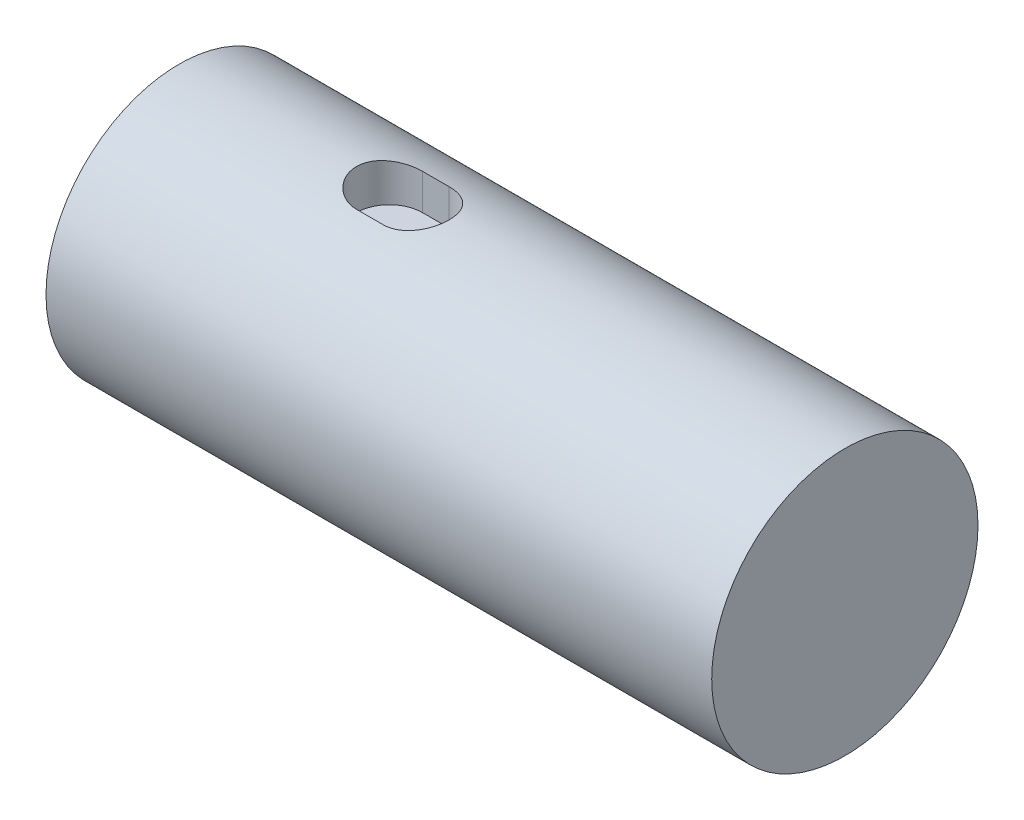
SolidWorks part; units mm, degrees
material "EN AW-AlMg4,5Mn0,7"
ref_plane "Přední rovina - XY" through (0, 0, 0) normal (0, 0, 1) x (1, 0, 0)
ref_plane "Horní rovina - XZ" through (0, 0, 0) normal (0, 1, 0) x (1, 0, 0)
ref_plane "Pravá rovina YZ" through (0, 0, 0) normal (1, 0, 0) x (0, 0, -1)
sketch "Skica1" plane through (0, 0, 0) normal (1, 0, 0) x (0, 0, -1)
  circle A0 centre (0, 0) radius 20
  point P3 (0, 20)
  dimension "D1" = 40
extrude "Vysunout1" add sketch "Skica1" along normal blind 100
ref_plane "Rovina1" through (0, 20, 0) normal (0, 1, 0) x (-1, 0, 0)
sketch "Skica2" plane through (0, 0, 0) normal (0, 1, 0) x (1, 0, 0)
  line L0 (31.5938, 0) -> (35.5924, 0) construction
  line L1 (31.5938, 4.9526) -> (35.5924, 4.9526)
  line L2 (31.5938, -4.9526) -> (35.5924, -4.9526)
  arc A0 (31.5938, 4.9526) -> (31.5938, -4.9526) centre (31.5938, 0) ccw
  arc A1 (35.5924, -4.9526) -> (35.5924, 4.9526) centre (35.5924, 0) ccw
  point P2 (33.5931, 0)
extrude "Vysunout2" cut sketch "Skica2" against normal blind 6 from surface at 20 starting at plane "Rovina1"
